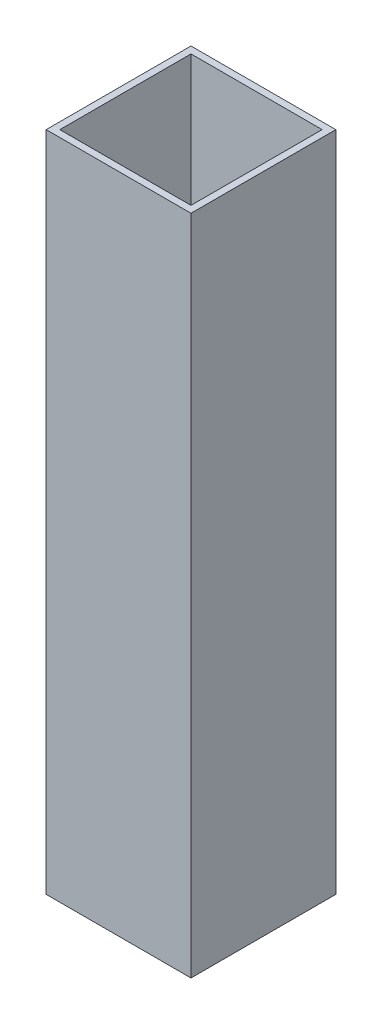
SolidWorks part; units mm, degrees
ref_plane "Alzado" through (0, 0, 0) normal (0, 0, 1) x (1, 0, 0)
ref_plane "Planta" through (0, 0, 0) normal (0, 1, 0) x (1, 0, 0)
ref_plane "Vista lateral" through (0, 0, 0) normal (1, 0, 0) x (0, 0, -1)
sketch "Sketch1" plane through (0, 0, 0) normal (0, 1, 0) x (1, 0, 0)
  line L0 (0, 0) -> (25.4, 0)
  line L1 (25.4, 0) -> (25.4, 25.4)
  line L2 (25.4, 25.4) -> (0, 25.4)
  line L3 (0, 25.4) -> (0, 0)
  line L4 (1.2, 24.2) -> (1.2, 1.2)
  line L5 (1.2, 1.2) -> (24.2, 1.2)
  line L6 (24.2, 1.2) -> (24.2, 24.2)
  line L7 (24.2, 24.2) -> (1.2, 24.2)
  dimension "D1" = 25.4
  dimension "D2" = 25.4
  dimension "D3" = 1.2
  dimension "D4" = 1.2
  dimension "D5" = 1.2
  dimension "D6" = 1.2
extrude "Boss-Extrude1" add sketch "Sketch1" along normal blind 116.14
